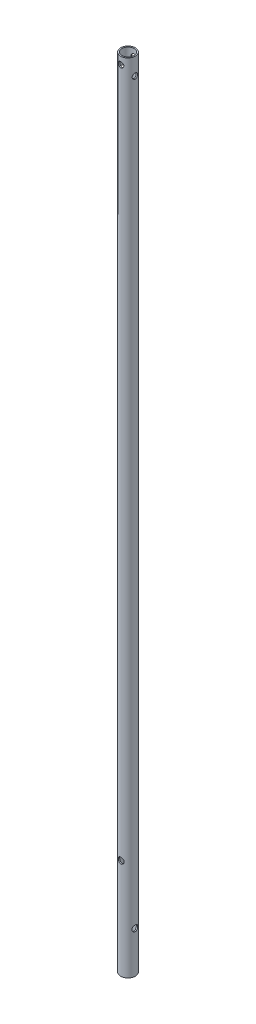
SolidWorks part; units mm, degrees
material "AISI 304"
ref_plane "Спереди" through (0, 0, 0) normal (0, 0, 1) x (1, 0, 0)
ref_plane "Сверху" through (0, 0, 0) normal (0, 1, 0) x (1, 0, 0)
ref_plane "Справа" through (0, 0, 0) normal (1, 0, 0) x (0, 0, -1)
sketch "Эскиз2" plane through (0, 0, 0) normal (0, 1, 0) x (1, 0, 0)
  circle A0 centre (0, 0) radius 15
  circle A1 centre (0, 0) radius 12.5
  dimension "D1" = 25
  dimension "D2" = 30
extrude "Бобышка-Вытянуть1" add sketch "Эскиз2" along normal blind 1630
sketch "Эскиз3" plane through (0, 0, 0) normal (0, 0, 1) x (1, 0, 0)
  line L0 (0, 1630) -> (0, 1615) construction
  line L1 (15, 1630) -> (-15, 1630) construction
  circle A0 centre (0, 1615) radius 5.5
  dimension "D1" = 11
  dimension "D2" = 15
extrude "Вырез-Вытянуть1" cut sketch "Эскиз3" against normal through all both and the other way through all
sketch "Эскиз4" plane through (0, 0, 0) normal (1, 0, 0) x (0, 0, -1)
  line L0 (0, 1630) -> (0, 1595) construction
  line L1 (12.5, 1630) -> (-12.5, 1630) construction
  circle A0 centre (0, 1595) radius 5.5
  dimension "D1" = 11
  dimension "D2" = 35
extrude "Вырез-Вытянуть2" cut sketch "Эскиз4" against normal through all both and the other way through all
sketch "Эскиз5" plane through (0, 0, 0) normal (0, 0, 1) x (1, 0, 0)
  line L0 (0, 0) -> (0, 205) construction
  line L1 (-200, 205) -> (200, 205) construction
  line L2 (-105, 85) -> (105, 85) construction
  line L3 (-15, 0) -> (15, 0) construction
  circle A0 centre (0, 205) radius 6
  point P4 (0, 85)
  dimension "D5" = 12
  dimension "D1" = 400
  dimension "D2" = 205
  dimension "D3" = 210
  dimension "D4" = 120
extrude "Вырез-Вытянуть3" cut sketch "Эскиз5" against normal through all both and the other way through all
sketch "Эскиз6" plane through (0, 0, 0) normal (1, 0, 0) x (0, 0, -1)
  line L0 (-15, 211) -> (-15, 199) construction
  line L1 (-15, 199) -> (15, 199) construction
  line L2 (15, 199) -> (15, 211) construction
  line L3 (-15, 205) -> (15, 205) construction
  line L4 (0, 205) -> (0, 85) construction
  circle A0 centre (0, 85) radius 6
  dimension "D2" = 12
  dimension "D1" = 120
extrude "Вырез-Вытянуть4" cut sketch "Эскиз6" against normal through all both and the other way through all
